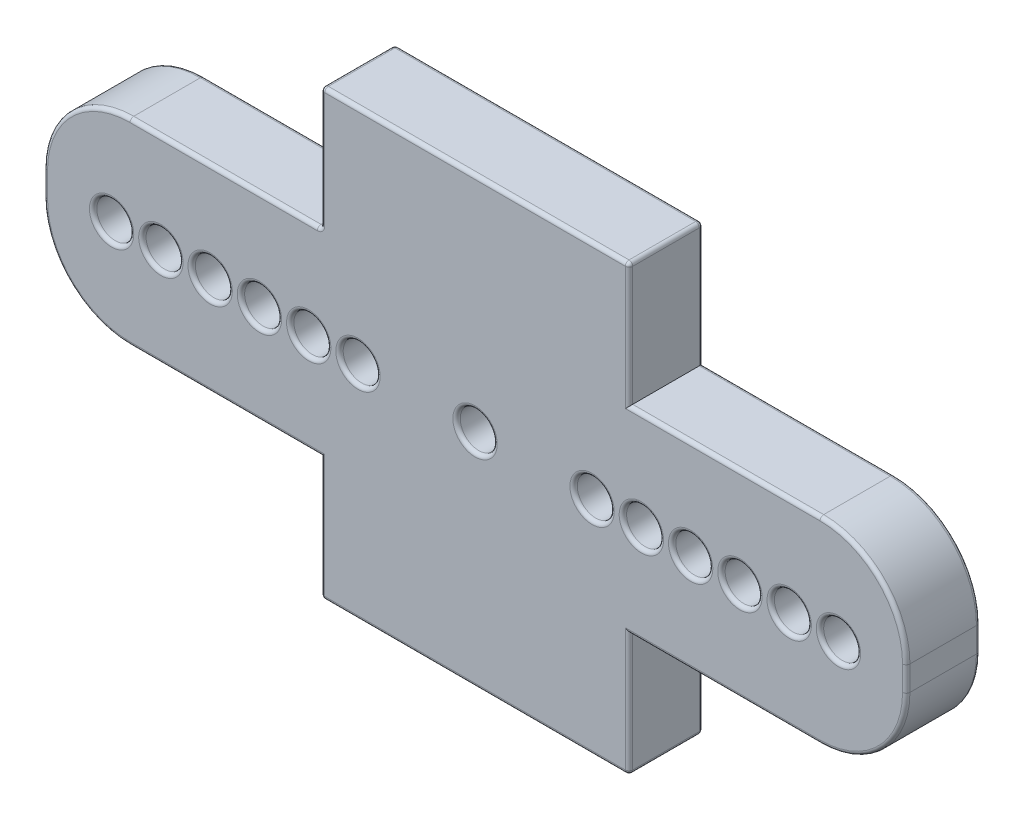
SolidWorks part; units mm, degrees
material "Balsa"
ref_plane "Front Plane" through (0, 0, 0) normal (0, 0, 1) x (1, 0, 0)
ref_plane "Top Plane" through (0, 0, 0) normal (0, 1, 0) x (1, 0, 0)
ref_plane "Right Plane" through (0, 0, 0) normal (1, 0, 0) x (0, 0, -1)
sketch "Sketch1" plane through (0, 0, 0) normal (0, 0, 1) x (1, 0, 0)
  line L0 (-17.5, 0.5) -> (-17.5, -0.5)
  line L1 (6.25, -9) -> (-6.25, -9) construction
  line L2 (6.25, -9) -> (6.25, 9) construction
  line L3 (6.25, 9) -> (-6.25, 9) construction
  line L4 (-6.25, -9) -> (-6.25, 9) construction
  line L5 (6.25, -9) -> (-6.25, 9) construction
  line L6 (6.25, 9) -> (-6.25, -9) construction
  line L7 (17.5, -4) -> (-17.5, -4) construction
  line L8 (17.5, -4) -> (17.5, 4) construction
  line L9 (17.5, 4) -> (-17.5, 4) construction
  line L10 (-17.5, -4) -> (-17.5, 4) construction
  line L11 (17.5, -4) -> (-17.5, 4) construction
  line L12 (17.5, 4) -> (-17.5, -4) construction
  line L13 (-14, -4) -> (-6.25, -4)
  line L14 (-6.25, -4) -> (-6.25, -9)
  line L15 (-6.25, -9) -> (6.25, -9)
  line L16 (6.25, -9) -> (6.25, -4)
  line L17 (6.25, -4) -> (14, -4)
  line L18 (17.5, -0.5) -> (17.5, 0.5)
  line L19 (14, 4) -> (6.25, 4)
  line L20 (6.25, 4) -> (6.25, 9)
  line L21 (6.25, 9) -> (-6.25, 9)
  line L22 (-6.25, 9) -> (-6.25, 4)
  line L23 (-6.25, 4) -> (-14, 4)
  circle A0 centre (0, 0) radius 0.75
  arc A1 (-14, 4) -> (-17.5, 0.5) centre (-14, 0.5) ccw
  arc A2 (-17.5, -0.5) -> (-14, -4) centre (-14, -0.5) ccw
  arc A3 (14, -4) -> (17.5, -0.5) centre (14, -0.5) ccw
  arc A4 (17.5, 0.5) -> (14, 4) centre (14, 0.5) ccw
  point P0 (0, 0)
  point P6 (0, 0)
  dimension "D5" = 1.5
  dimension "D6" = 3.5
  dimension "D1" = 8
  dimension "D2" = 35
  dimension "D3" = 12.5
  dimension "D4" = 18
extrude "Boss-Extrude2" add sketch "Sketch1" along normal mid plane 3
sketch "Sketch2" plane through (0, 0, 1.5) normal (0, 0, 1) x (1, 0, 0)
  line L0 (-17.5, 0) -> (17.5, 0) construction
  line L1 (-17.5, 0.5) -> (-17.5, -0.5) construction
  line L2 (17.5, -0.5) -> (17.5, 0.5) construction
  line L5 (6.25, -9) -> (6.25, -4) construction
  line L6 (-6.25, -9) -> (6.25, -9) construction
  circle A0 centre (-14.75, 0) radius 0.75
  circle A1 centre (-12.75, 0) radius 0.75
  circle A2 centre (-10.75, 0) radius 0.75
  circle A3 centre (-8.75, 0) radius 0.75
  circle A4 centre (-6.75, 0) radius 0.75
  circle A5 centre (-4.75, 0) radius 0.75
  point P7 (-4.75, 0)
  point P8 (-6.75, 0)
  point P9 (-8.75, 0)
  point P10 (-10.75, 0)
  point P11 (-12.75, 0)
  point P12 (-14.75, 0)
  dimension "D8" = 1.5
  dimension "D1" = 4.75
  dimension "D2" = 2.75
  dimension "D7" = 6
extrude "Cut-Extrude1" cut sketch "Sketch2" against normal up to next (3 mm away)
mirror "Mirror1" about plane through (0, 0, 0) normal (1, 0, 0) of "Cut-Extrude1"
fillet "Fillet2" radius 0.15 63 edges at (4, 0, 1.5) (5.5, 0, -1.5) (6, 0, 1.5) (7.5, 0, -1.5) (8, 0, 1.5) (9.5, 0, -1.5) (10, 0, 1.5) (11.5, 0, -1.5) (12, 0, 1.5) (13.5, 0, -1.5) (14, 0, 1.5) (15.5, 0, -1.5) (-4, 0, -1.5) (-4, 0, 1.5) (-6, 0, -1.5) (-6, 0, 1.5) (-8, 0, -1.5) (-8, 0, 1.5) (-10, 0, -1.5) (-10, 0, 1.5) (-12, 0, -1.5) (-12, 0, 1.5) (-14, 0, -1.5) (-14, 0, 1.5) (0.75, 0, -1.5) (0.75, 0, 1.5) (-6.25, 6.5, -1.5) (-10.125, 4, -1.5) (-17.5, 0, -1.5) (-10.125, -4, -1.5) (-6.25, -6.5, -1.5) (0, -9, -1.5) (6.25, -6.5, -1.5) (10.125, -4, -1.5) (17.5, 0, -1.5) (10.125, 4, -1.5) (6.25, 6.5, -1.5) (0, 9, -1.5) (-10.125, 4, 1.5) (-17.5, 0, 1.5) (-10.125, -4, 1.5) (-6.25, -6.5, 1.5) (0, -9, 1.5) (6.25, -6.5, 1.5) (10.125, -4, 1.5) (17.5, 0, 1.5) (10.125, 4, 1.5) (6.25, 6.5, 1.5) (0, 9, 1.5) (-6.25, 9, 0) (6.25, 9, 0) (6.25, -9, 0) (-6.25, -9, 0) (-6.25, 6.5, 1.5) (-6.25, 4, 0) (-16.4749, 2.9749, -1.5) (-16.4749, -2.9749, -1.5) (16.4749, -2.9749, -1.5) (16.4749, 2.9749, -1.5) (-16.4749, 2.9749, 1.5) (-16.4749, -2.9749, 1.5) (16.4749, -2.9749, 1.5) (16.4749, 2.9749, 1.5)
